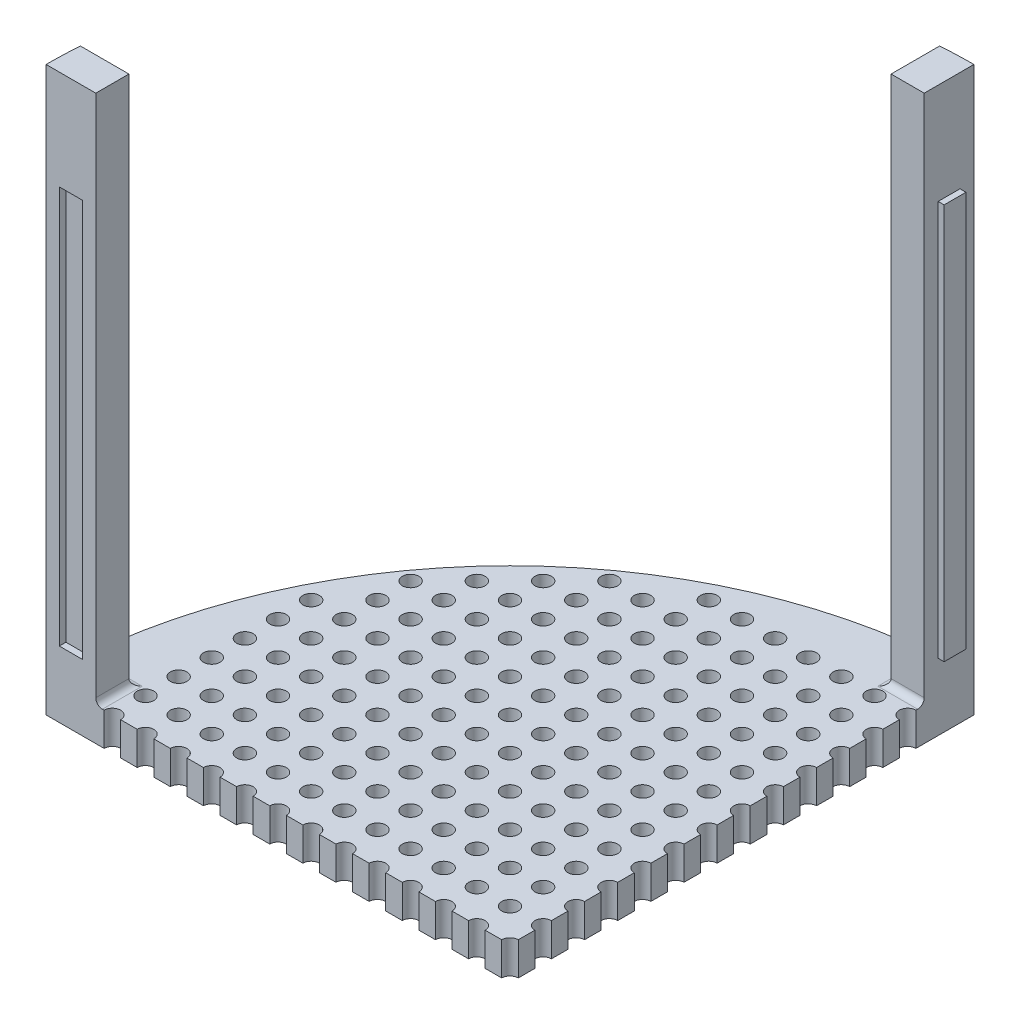
SolidWorks part; units mm, degrees
ref_plane "Front Plane" through (0, 0, 0) normal (0, 0, 1) x (1, 0, 0)
ref_plane "Top Plane" through (0, 0, 0) normal (0, 1, 0) x (1, 0, 0)
ref_plane "Right Plane" through (0, 0, 0) normal (1, 0, 0) x (0, 0, -1)
sketch "Sketch1" plane through (0, 0, 0) normal (0, 1, 0) x (1, 0, 0)
  line L1 (0, 0) -> (177.8, 0)
  line L4 (177.8, 0) -> (177.8, 177.8)
  arc A0 (177.8, 177.8) -> (0, 0) centre (177.8, 0) ccw
  dimension "D2" = 177.8
extrude "Boss-Extrude1" add sketch "Sketch1" along normal blind 12.7
sketch "Sketch3" plane through (0, 12.7, 0) normal (0, 1, 0) x (1, 0, 0)
  line L0 (19.05, 0) -> (19.05, 12.7)
  line L1 (19.05, 12.7) -> (0.4542, 12.7)
  line L2 (0, 0) -> (177.8, 0)
  line L3 (177.8, 0) -> (177.8, 177.8)
  line L4 (0, 0) -> (19.05, 0)
  line L5 (177.8, 158.75) -> (177.8, 177.8)
  line L6 (177.8, 158.75) -> (165.1, 158.75)
  line L7 (165.1, 158.75) -> (165.1, 177.3458)
  arc A0 (0.4542, 12.7) -> (0, 0) centre (177.8, 0) ccw
  arc A1 (177.8, 177.8) -> (0, 0) centre (177.8, 0) ccw
  arc A2 (177.8, 177.8) -> (165.1, 177.3458) centre (177.8, 0) ccw
  dimension "D2" = 19.05
  dimension "D3" = 12.7
  dimension "D4" = 19.05
  dimension "D5" = 12.7
  dimension "D1" = 0
extrude "Boss-Extrude2" add sketch "Sketch3" along normal blind 203.2 contours L6 L7 A2 L5
sketch "Sketch4" plane through (0, 12.7, 0) normal (0, 1, 0) x (1, 0, 0)
  line L2 (19.05, 0) -> (177.8, 0) construction
  line L4 (177.8, 0) -> (177.8, 158.75) construction
  circle A0 centre (177.8, 0) radius 3.175
  dimension "D1" = 6.35
extrude "Cut-Extrude1" cut sketch "Sketch4" against normal blind 254
pattern_linear "LPattern1" count 13 spacing 12.7 along (0, 0, -1) count 13 spacing 12.7 along (-1, 0, 0) skipping (7, 12), (9, 11), (10, 10), (11, 9), (12, 7), (12, 8) of "Cut-Extrude1"
sketch "Sketch5" plane through (0, 0, 0) normal (0, 0, 1) x (1, 0, 0)
  line L0 (0, 215.9) -> (0, 0) construction
  line L1 (5.08, 177.8) -> (13.97, 177.8)
  line L2 (5.08, 177.8) -> (5.08, 25.4)
  line L3 (5.08, 25.4) -> (13.97, 25.4)
  line L4 (13.97, 177.8) -> (13.97, 25.4)
  line L5 (19.05, 215.9) -> (19.05, 12.7) construction
  line L6 (0, 0) -> (22.225, 0) construction
  point P8 (9.525, 25.4)
  dimension "D1" = 5.08
  dimension "D2" = 5.08
  dimension "D3" = 152.4
  dimension "D4" = 25.4
extrude "Cut-Extrude2" cut sketch "Sketch5" against normal blind 2.54
sketch "Sketch6" plane through (177.8, 0, 0) normal (1, 0, 0) x (0, 0, -1)
  line L0 (177.8, 215.9) -> (177.8, 0) construction
  line L1 (164.084, 177.292) -> (172.466, 177.292)
  line L2 (164.084, 177.292) -> (164.084, 25.654)
  line L3 (164.084, 25.654) -> (172.466, 25.654)
  line L4 (172.466, 177.292) -> (172.466, 25.654)
  line L5 (158.75, 215.9) -> (158.75, 12.7) construction
  line L6 (155.575, 0) -> (177.8, 0) construction
  dimension "D1" = 5.334
  dimension "D2" = 5.334
  dimension "D3" = 25.654
  dimension "D4" = 151.638
extrude "Boss-Extrude3" add sketch "Sketch6" along normal blind 2.286
sketch "Sketch7" plane through (0, 215.9, 0) normal (0, 1, 0) x (1, 0, 0)
  line L0 (0.4542, 12.7) -> (165.1, 177.3458)
  line L1 (0, 0) -> (177.8, 0)
  line L2 (177.8, 0) -> (177.8, 177.8)
  arc A0 (0.4542, 12.7) -> (0, 0) centre (177.8, 0) ccw construction
  arc A1 (177.8, 177.8) -> (165.1, 177.3458) centre (177.8, 0) ccw construction
  arc A2 (0.4542, 12.7) -> (0, 0) centre (177.8, 0) ccw
  arc A3 (177.8, 177.8) -> (165.1, 177.3458) centre (177.8, 0) ccw
fillet "Fillet1" radius 2.54 4 edges at (19.05, 12.7, -6.35) (9.7521, 12.7, -12.7) (171.45, 12.7, -158.75) (165.1, 12.7, -168.0479)
